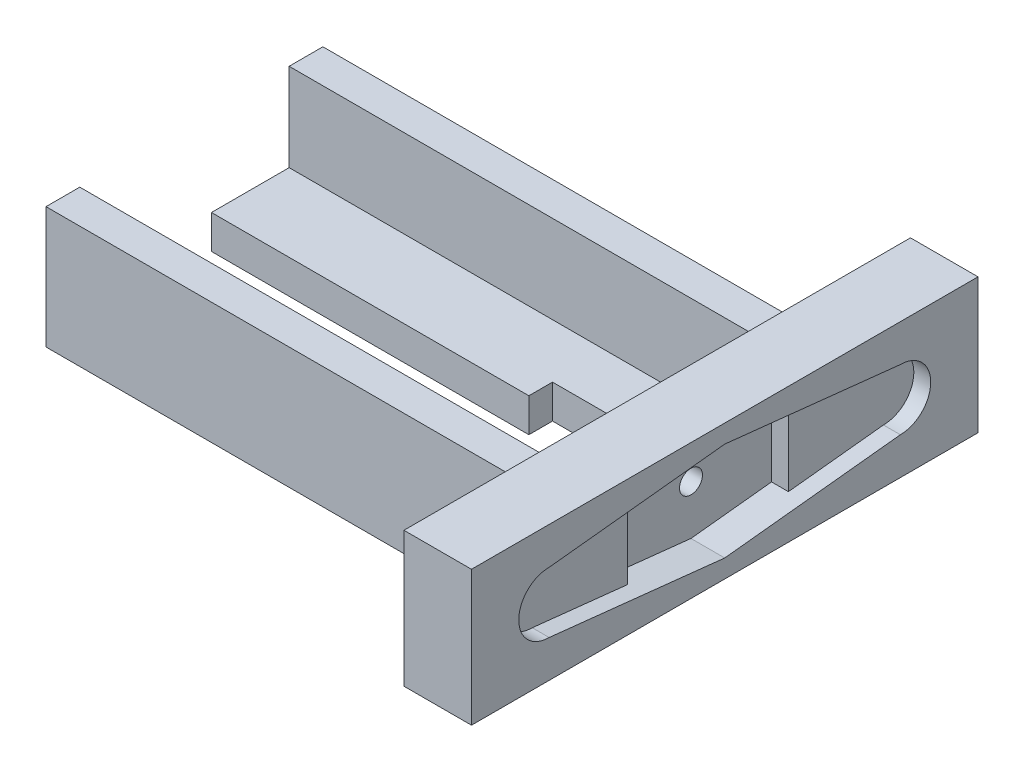
SolidWorks part; units mm, degrees
ref_plane "Front" through (0, 0, 0) normal (0, 0, 1) x (1, 0, 0)
ref_plane "Top" through (0, 0, 0) normal (0, 1, 0) x (1, 0, 0)
ref_plane "Right" through (0, 0, 0) normal (1, 0, 0) x (0, 0, -1)
sketch "草图1" plane through (0, 0, 0) normal (0, 1, 0) x (1, 0, 0)
  line L1 (0, 0) -> (10, 0)
  line L2 (0, 0) -> (0, 75)
  line L3 (0, 75) -> (10, 75)
  line L4 (10, 0) -> (10, 75)
  dimension "D1" = 75
  dimension "D2" = 10
extrude "凸台-拉伸2" add sketch "草图1" along normal blind 20 contours L3 L4 L1 L2
sketch "草图5" plane through (10, 0, 0) normal (1, 0, 0) x (0, 0, -1)
  line L1 (75, 0) -> (75, 20)
  line L14 (11.5, 14.5) -> (37.5, 17.3)
  line L15 (37.5, 17.3) -> (63.5, 14.5)
  line L16 (63.5, 5.5) -> (37.5, 2.7)
  line L17 (37.5, 2.7) -> (11.5, 5.5)
  line L19 (0, 20) -> (0, 0) construction
  circle A0 centre (37.5, 10) radius 7.3
  arc A3 (11.5, 14.5) -> (11.5, 5.5) centre (11.5, 10) ccw
  arc A4 (63.5, 14.5) -> (63.5, 5.5) centre (63.5, 10) cw
  dimension "D1" = 26
  dimension "D4" = 75
  dimension "D2" = 26
  dimension "D3" = 37.5
sketch "草图10" plane through (0, 0, 0) normal (-1, 0, 0) x (0, 0, 1)
  line L0 (-75, 20) -> (-75, 0) construction
  line L1 (-53, 5) -> (-22, 5)
  line L2 (-53, 5) -> (-53, 0)
  line L3 (-53, 0) -> (-22, 0)
  line L4 (-22, 5) -> (-22, 0)
  line L5 (0, 0) -> (-75, 0) construction
  dimension "D1" = 31
  dimension "D2" = 5
  dimension "D3" = 22
  dimension "D4" = 0
extrude "凸台-拉伸3" add sketch "草图10" along normal blind 70
sketch "草图11" plane through (0, 0, 0) normal (-1, 0, 0) x (0, 0, 1)
  line L1 (-22, 0) -> (-17, 0)
  line L2 (-22, 0) -> (-22, 18)
  line L3 (-22, 18) -> (-17, 18)
  line L4 (-17, 0) -> (-17, 18)
  dimension "D1" = 5
  dimension "D2" = 18
extrude "凸台-拉伸4" add sketch "草图11" along normal blind 70
sketch "草图12" plane through (0, 0, 0) normal (-1, 0, 0) x (0, 0, 1)
  line L1 (-53, 0) -> (-58, 0)
  line L2 (-53, 0) -> (-53, 18)
  line L3 (-53, 18) -> (-58, 18)
  line L4 (-58, 0) -> (-58, 18)
  dimension "D1" = 18
  dimension "D2" = 5
extrude "凸台-拉伸5" add sketch "草图12" along normal blind 70
sketch "草图13" plane through (0, 5, 0) normal (0, 1, 0) x (1, 0, 0)
  line L0 (-70, 22) -> (-70, 53) construction
  line L5 (-70, 41.5) -> (-10, 41.5)
  line L6 (-70, 41.5) -> (-70, 33.5)
  line L7 (-70, 33.5) -> (-10, 33.5)
  line L8 (-10, 41.5) -> (-10, 33.5)
  line L9 (-70, 53) -> (0, 53) construction
  dimension "D1" = 60
  dimension "D2" = 8
  dimension "D3" = 11.5
extrude "切除-拉伸6" cut sketch "草图13" against normal blind 20
sketch "草图14" plane through (0, 5, 0) normal (0, 1, 0) x (1, 0, 0)
  line L1 (-23, 45) -> (-13, 45)
  line L2 (-23, 45) -> (-23, 41.5)
  line L3 (-23, 41.5) -> (-13, 41.5)
  line L4 (-13, 45) -> (-13, 41.5)
  line L5 (0, 22) -> (0, 53) construction
  line L7 (-10, 41.5) -> (-70, 41.5) construction
  dimension "D1" = 10
  dimension "D2" = 3.5
  dimension "D3" = 13
  dimension "D4" = 0
extrude "切除-拉伸7" cut sketch "草图14" against normal blind 20
hole_wizard "M3 凹圆头螺钉的柱形沉头孔1" positions "3D草图1" profile "草图15" counterbore size "M3" standard "ANSI Metric"
sketch3d "3D草图1"
  line L1 (0, 20, 0) -> (0, 20, -75) construction
  line L2 (0, 20, -75) -> (0, 0, -75) construction
  point P0 (0, 10, -37.5)
  dimension "D1" = 10
  dimension "D2" = 37.5
sketch "草图15" plane through (0, 10, -37.5) normal (0, 1, 0) x (0, 0, 1)
  line L0 (0, 0) -> (0, 21.0215)
  line L1 (0, 21.0215) -> (1.7, 20)
  line L2 (1.7, 20) -> (1.7, 1.65)
  line L3 (1.7, 1.65) -> (3.35, 1.65)
  line L4 (3.35, 1.65) -> (3.35, 0)
  line L5 (3.35, 0) -> (0, 0)
  line L10 (0, 21.0215) -> (-1.7, 20) construction
  line L11 (0, -6.35) -> (0, 107.95) construction
  dimension "孔直径" = 3.4
  dimension "孔深度" = 20
  dimension "柱形沉头孔直径" = 6.7
  dimension "柱形沉头孔深度" = 1.65
  dimension "导头角度" = 118
extrude "切除-拉伸8" cut sketch "草图5" against normal blind 2.5 contours A4 L15 A0 L16 | L14 A0 L17 L16 L15 | L14 A3 L17 A0
sketch "草图16" plane through (10, 0, 0) normal (1, 0, 0) x (0, 0, -1)
  line L0 (37.5, 17.3) -> (25.569, 16.0151)
  line L1 (11.5, 14.5) -> (37.5, 17.3) construction
  line L2 (25.569, 16.0151) -> (25.569, 3.9849)
  line L3 (37.5, 2.7) -> (11.5, 5.5) construction
  line L4 (25.569, 3.9849) -> (37.5, 2.7)
  line L5 (37.5, 2.7) -> (49.431, 3.9849)
  line L6 (63.5, 5.5) -> (37.5, 2.7) construction
  line L7 (49.431, 3.9849) -> (49.431, 16.0151)
  line L8 (37.5, 17.3) -> (63.5, 14.5) construction
  line L9 (49.431, 16.0151) -> (37.5, 17.3)
  dimension "D1" = 12
  dimension "D2" = 12
extrude "切除-拉伸9" cut sketch "草图16" against normal blind 5
